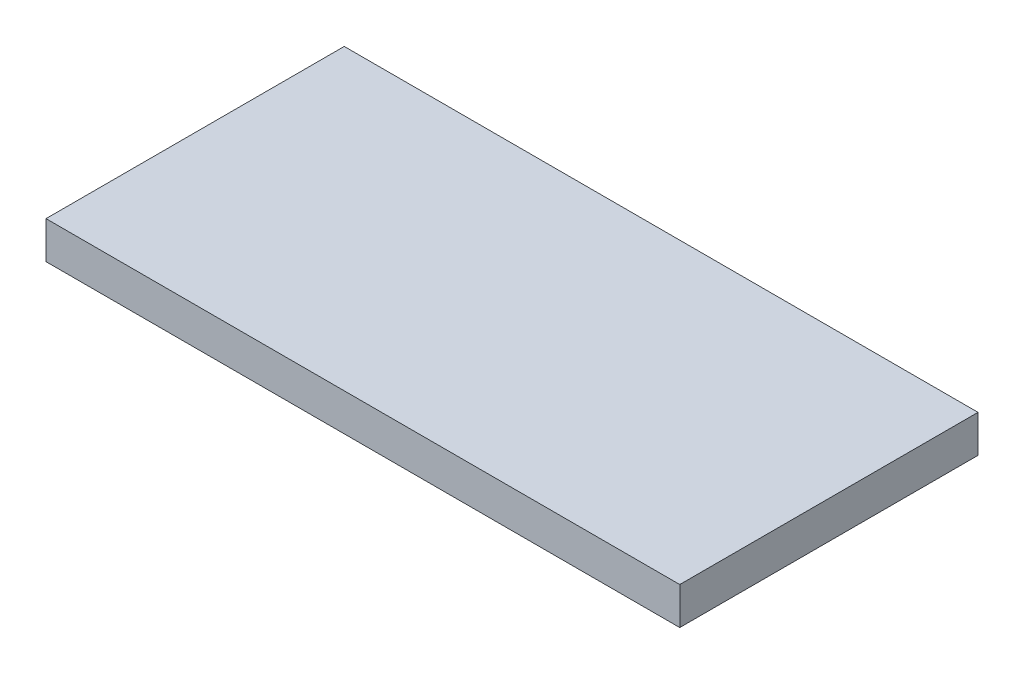
SolidWorks part; units mm, degrees
ref_plane "Alzado" through (0, 0, 0) normal (0, 0, 1) x (1, 0, 0)
ref_plane "Planta" through (0, 0, 0) normal (0, 1, 0) x (1, 0, 0)
ref_plane "Vista lateral" through (0, 0, 0) normal (1, 0, 0) x (0, 0, -1)
sketch "Croquis1" plane through (0, 0, 0) normal (0, 1, 0) x (1, 0, 0)
  line L1 (-40.8626, 12.4885) -> (44.1374, 12.4885)
  line L2 (-40.8626, 12.4885) -> (-40.8626, -27.5115)
  line L3 (-40.8626, -27.5115) -> (44.1374, -27.5115)
  line L4 (44.1374, 12.4885) -> (44.1374, -27.5115)
  dimension "D1" = 40
  dimension "D2" = 85
extrude "Saliente-Extruir1" add sketch "Croquis1" along normal blind 5
